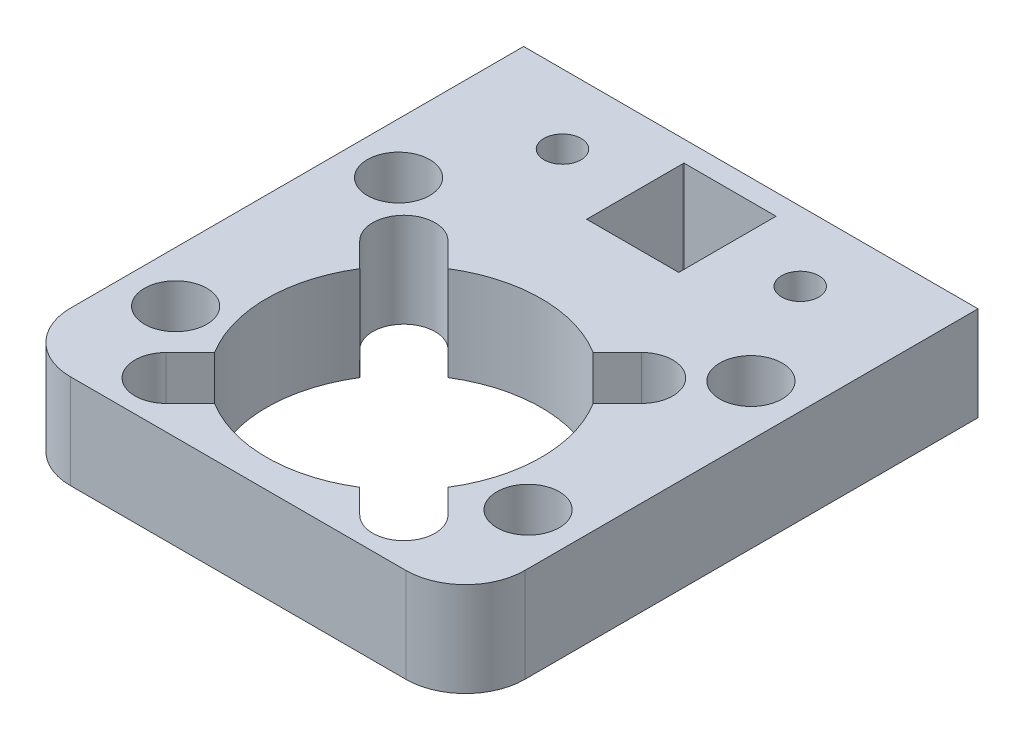
SolidWorks part; units mm, degrees
ref_plane "Front" through (0, 0, 0) normal (0, 0, 1) x (1, 0, 0)
ref_plane "Top" through (0, 0, 0) normal (0, 1, 0) x (1, 0, 0)
ref_plane "Right" through (0, 0, 0) normal (1, 0, 0) x (0, 0, -1)
ref_plane "Plane1" through (0, 6.35, 0) normal (0, 1, 0) x (1, 0, 0)
sketch "Sketch1" plane through (0, 6.35, 0) normal (0, 1, 0) x (1, 0, 0)
  line L0 (-15.289, 23.35) -> (-15.289, -7.15)
  line L1 (-11.289, -11.15) -> (11.289, -11.15)
  line L2 (15.289, -7.15) -> (15.289, 23.35)
  line L3 (15.289, 23.35) -> (-15.289, 23.35)
  line L4 (-3.1001, 15.4) -> (-3.1, 15.5)
  line L5 (-3.1, 15.5) -> (-3.1, 21.85)
  line L6 (-3.1, 21.85) -> (-3.1, 21.95)
  line L7 (-3.1, 21.95) -> (3.1, 21.9477)
  line L8 (3.1, 21.9477) -> (3.1, 15.5)
  line L9 (3.1, 15.5) -> (3.1001, 15.4)
  line L10 (3.1001, 15.4) -> (-3.1001, 15.4)
  arc A0 (-15.289, -7.15) -> (-11.289, -11.15) centre (-11.289, -7.15) ccw
  arc A1 (11.289, -11.15) -> (15.289, -7.15) centre (11.289, -7.15) ccw
extrude "Boss-Extrude1" add sketch "Sketch1" against normal blind 6.35
sketch "Sketch2" plane through (0, 0, 0) normal (0, -1, 0) x (1, 0, 0)
  line L0 (4.885, -7.8549) -> (6.5151, -9.4849)
  line L1 (9.4849, -6.5151) -> (7.8549, -4.885)
  line L2 (7.8549, 4.885) -> (9.4849, 6.5151)
  line L3 (6.5151, 9.4849) -> (4.885, 7.8549)
  line L4 (-4.885, 7.8549) -> (-6.5151, 9.4849)
  line L5 (-9.4849, 6.5151) -> (-7.8549, 4.885)
  line L6 (-7.8549, -4.885) -> (-9.4849, -6.5151)
  line L7 (-6.5151, -9.4849) -> (-4.885, -7.8549)
  arc A0 (6.5151, -9.4849) -> (9.4849, -6.5151) centre (8, -8) ccw
  arc A1 (7.8549, -4.885) -> (7.8549, 4.885) centre (0, 0) ccw
  arc A2 (9.4849, 6.5151) -> (6.5151, 9.4849) centre (8, 8) ccw
  arc A3 (4.885, 7.8549) -> (-4.885, 7.8549) centre (0, 0) ccw
  arc A4 (-6.5151, 9.4849) -> (-9.4849, 6.5151) centre (-8, 8) ccw
  arc A5 (-7.8549, 4.885) -> (-7.8549, -4.885) centre (0, 0) ccw
  arc A6 (-9.4849, -6.5151) -> (-6.5151, -9.4849) centre (-8, -8) ccw
  arc A7 (-4.885, -7.8549) -> (4.885, -7.8549) centre (0, 0) ccw
extrude "Cut-Extrude1" cut sketch "Sketch2" against normal through all
hole_wizard "Ø2.5 (2.5) Diameter Hole1" positions "Sketch4" profile "Sketch3" hole size "Ø2.5" standard "ANSI Metric"
sketch "Sketch4" plane through (0, 0, 0) normal (0, -1, 0) x (-1, 0, 0)
  point P0 (8, 18.675)
sketch "Sketch3" plane through (-8, 0, -18.675) normal (1, 0, 0) x (0, 0, -1)
  line L0 (0, 0) -> (0, 6.35)
  line L1 (0, 6.35) -> (1.25, 6.35)
  line L2 (1.25, 6.35) -> (1.25, 0)
  line L5 (1.25, 0) -> (0, 0)
  line L11 (0, -6.35) -> (0, 107.95) construction
  dimension "Thru Hole Dia." = 2.5
  dimension "Thru Hole Depth" = 6.35
hole_wizard "Ø2.5 (2.5) Diameter Hole2" positions "Sketch6" profile "Sketch5" hole size "Ø2.5" standard "ANSI Metric"
sketch "Sketch6" plane through (0, 0, 0) normal (0, -1, 0) x (-1, 0, 0)
  point P0 (-8, 18.675)
sketch "Sketch5" plane through (8, 0, -18.675) normal (1, 0, 0) x (0, 0, -1)
  line L0 (0, 0) -> (0, 6.35)
  line L1 (0, 6.35) -> (1.25, 6.35)
  line L2 (1.25, 6.35) -> (1.25, 0)
  line L5 (1.25, 0) -> (0, 0)
  line L11 (0, -6.35) -> (0, 107.95) construction
  dimension "Thru Hole Dia." = 2.5
  dimension "Thru Hole Depth" = 6.35
hole_wizard "Ø4.2 (4.2) Diameter Hole1" positions "Sketch8" profile "Sketch7" hole size "Ø4.2" standard "ANSI Metric"
sketch "Sketch8" plane through (0, 0, 0) normal (0, -1, 0) x (-1, 0, 0)
  point P0 (-11.8586, 11.5)
sketch "Sketch7" plane through (11.8586, 0, -11.5) normal (1, 0, 0) x (0, 0, -1)
  line L0 (0, 0) -> (0, 6.35)
  line L1 (0, 6.35) -> (2.1, 6.35)
  line L2 (2.1, 6.35) -> (2.1, 0)
  line L5 (2.1, 0) -> (0, 0)
  line L11 (0, -6.35) -> (0, 107.95) construction
  dimension "Thru Hole Dia." = 4.2
  dimension "Thru Hole Depth" = 6.35
hole_wizard "Ø4.2 (4.2) Diameter Hole2" positions "Sketch10" profile "Sketch9" hole size "Ø4.2" standard "ANSI Metric"
sketch "Sketch10" plane through (0, 0, 0) normal (0, -1, 0) x (-1, 0, 0)
  point P0 (11.8586, 11.5)
sketch "Sketch9" plane through (-11.8586, 0, -11.5) normal (1, 0, 0) x (0, 0, -1)
  line L0 (0, 0) -> (0, 6.35)
  line L1 (0, 6.35) -> (2.1, 6.35)
  line L2 (2.1, 6.35) -> (2.1, 0)
  line L5 (2.1, 0) -> (0, 0)
  line L11 (0, -6.35) -> (0, 107.95) construction
  dimension "Thru Hole Dia." = 4.2
  dimension "Thru Hole Depth" = 6.35
hole_wizard "Ø4.2 (4.2) Diameter Hole3" positions "Sketch12" profile "Sketch11" hole size "Ø4.2" standard "ANSI Metric"
sketch "Sketch12" plane through (0, 0, 0) normal (0, -1, 0) x (-1, 0, 0)
  point P0 (-11.8596, -3.5)
sketch "Sketch11" plane through (11.8596, 0, 3.5) normal (1, 0, 0) x (0, 0, -1)
  line L0 (0, 0) -> (0, 6.35)
  line L1 (0, 6.35) -> (2.1, 6.35)
  line L2 (2.1, 6.35) -> (2.1, 0)
  line L5 (2.1, 0) -> (0, 0)
  line L11 (0, -6.35) -> (0, 107.95) construction
  dimension "Thru Hole Dia." = 4.2
  dimension "Thru Hole Depth" = 6.35
hole_wizard "Ø4.2 (4.2) Diameter Hole4" positions "Sketch14" profile "Sketch13" hole size "Ø4.2" standard "ANSI Metric"
sketch "Sketch14" plane through (0, 0, 0) normal (0, -1, 0) x (-1, 0, 0)
  point P0 (11.8596, -3.5)
sketch "Sketch13" plane through (-11.8596, 0, 3.5) normal (1, 0, 0) x (0, 0, -1)
  line L0 (0, 0) -> (0, 6.35)
  line L1 (0, 6.35) -> (2.1, 6.35)
  line L2 (2.1, 6.35) -> (2.1, 0)
  line L5 (2.1, 0) -> (0, 0)
  line L11 (0, -6.35) -> (0, 107.95) construction
  dimension "Thru Hole Dia." = 4.2
  dimension "Thru Hole Depth" = 6.35
